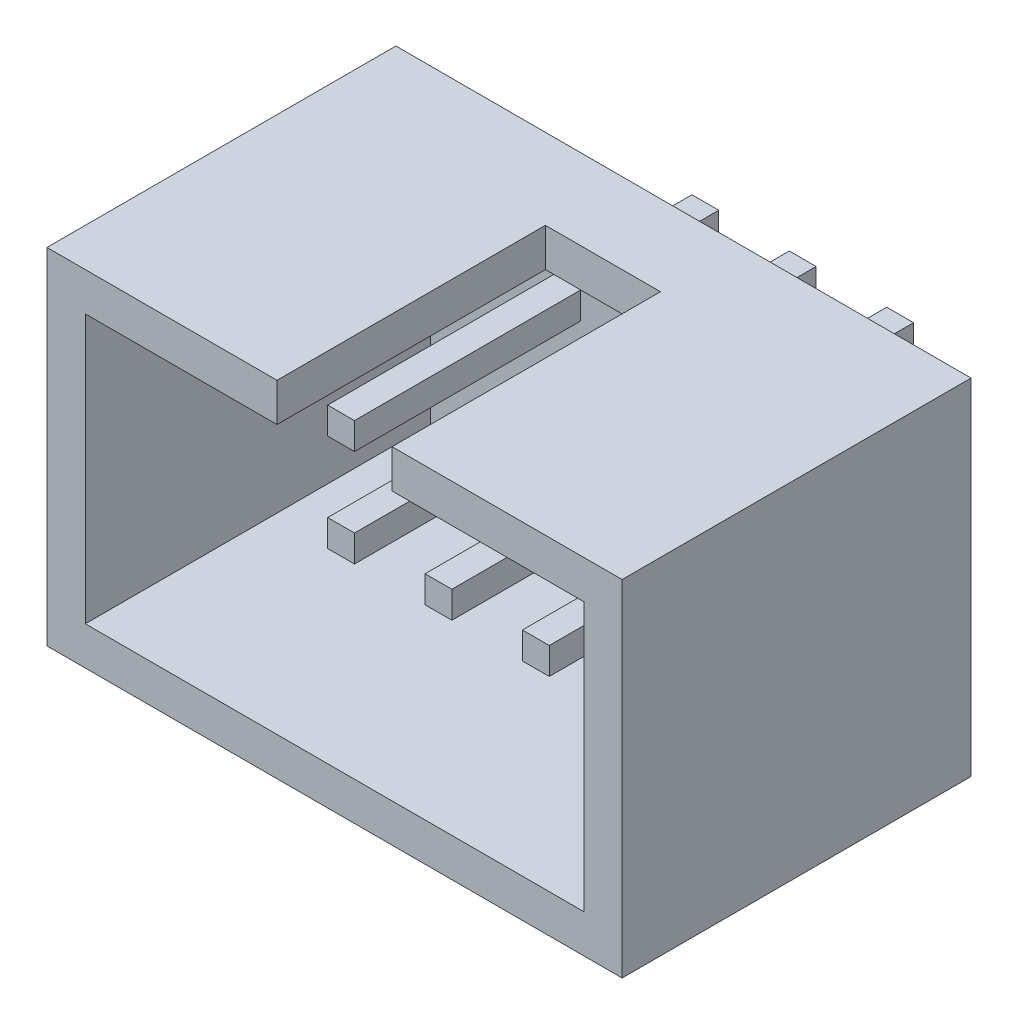
SolidWorks part; units mm, degrees
ref_plane "Alzado" through (0, 0, 0) normal (0, 0, 1) x (1, 0, 0)
ref_plane "Planta" through (0, 0, 0) normal (0, 1, 0) x (1, 0, 0)
ref_plane "Vista lateral" through (0, 0, 0) normal (1, 0, 0) x (0, 0, -1)
sketch "Croquis1" plane through (0, 0, 0) normal (0, 0, 1) x (1, 0, 0)
  line L13 (-6.5, -3.5) -> (-6.5, 3.5)
  line L14 (-7.5, -4.5) -> (7.5, -4.5)
  line L15 (-7.5, -4.5) -> (-7.5, 4.5)
  line L16 (-7.5, 4.5) -> (7.5, 4.5)
  line L17 (7.5, -4.5) -> (7.5, 4.5)
  line L18 (-7.5, -4.5) -> (7.5, 4.5) construction
  line L19 (-7.5, 4.5) -> (7.5, -4.5) construction
  line L20 (-6.5, 3.5) -> (6.5, 3.5)
  line L21 (6.5, -3.5) -> (6.5, 3.5)
  line L22 (-6.5, -3.5) -> (6.5, -3.5)
  point P0 (0, 0)
  dimension "D1" = 15
  dimension "D2" = 9
  dimension "D3" = 1
extrude "Saliente-Extruir1" add sketch "Croquis1" along normal blind 9
sketch "Croquis2" plane through (0, 0, 0) normal (0, 0, -1) x (-1, 0, 0)
  line L1 (-7.5, -4.5) -> (7.5, -4.5)
  line L2 (-7.5, -4.5) -> (-7.5, 4.5)
  line L3 (-7.5, 4.5) -> (7.5, 4.5)
  line L4 (7.5, -4.5) -> (7.5, 4.5)
  line L5 (-7.5, -4.5) -> (7.5, 4.5) construction
  line L6 (-7.5, 4.5) -> (7.5, -4.5) construction
  point P0 (0, 0)
extrude "Saliente-Extruir2" add sketch "Croquis2" along normal blind 0.1
sketch "Croquis3" plane through (0, 0, 9) normal (0, 0, 1) x (1, 0, 0)
  line L0 (6.5, 3.5) -> (-6.5, 3.5) construction
  line L1 (-1.5, 1.7962) -> (1.5, 1.7962)
  line L2 (-1.5, 1.7962) -> (-1.5, 5.2038)
  line L3 (-1.5, 5.2038) -> (1.5, 5.2038)
  line L4 (1.5, 1.7962) -> (1.5, 5.2038)
  line L5 (-1.5, 1.7962) -> (1.5, 5.2038) construction
  line L6 (-1.5, 5.2038) -> (1.5, 1.7962) construction
  point P0 (0, 3.5)
  point P7 (0, 3.5)
  dimension "D1" = 3
extrude "Cortar-Extruir1" cut sketch "Croquis3" against normal blind 7
sketch "Croquis4" plane through (0, 0, -0.1) normal (0, 0, -1) x (-1, 0, 0)
  line L0 (-7.5, 4.5) -> (-7.5, -4.5) construction
  line L1 (-2.5, 1.5) -> (-1.8, 1.5)
  line L2 (-2.5, 1.5) -> (-2.5, 0.8)
  line L3 (-2.5, 0.8) -> (-1.8, 0.8)
  line L4 (-1.8, 1.5) -> (-1.8, 0.8)
  line L5 (-2.5, 1.5) -> (-1.8, 0.8) construction
  line L6 (-2.5, 0.8) -> (-1.8, 1.5) construction
  line L7 (7.5, 4.5) -> (-7.5, 4.5) construction
  line L8 (0.04, 1.5) -> (0.04, 0.8)
  line L9 (0.04, 1.5) -> (0.74, 1.5)
  line L10 (0.74, 1.5) -> (0.74, 0.8)
  line L11 (0.04, 0.8) -> (0.74, 0.8)
  line L12 (2.58, 1.5) -> (2.58, 0.8)
  line L13 (2.58, 1.5) -> (3.28, 1.5)
  line L14 (3.28, 1.5) -> (3.28, 0.8)
  line L15 (2.58, 0.8) -> (3.28, 0.8)
  line L16 (0.04, -1.04) -> (0.04, -1.74)
  line L17 (0.04, -1.04) -> (0.74, -1.04)
  line L18 (0.74, -1.04) -> (0.74, -1.74)
  line L19 (0.04, -1.74) -> (0.74, -1.74)
  line L20 (2.58, -1.04) -> (2.58, -1.74)
  line L21 (2.58, -1.04) -> (3.28, -1.04)
  line L22 (3.28, -1.04) -> (3.28, -1.74)
  line L23 (2.58, -1.74) -> (3.28, -1.74)
  line L24 (-2.5, -1.04) -> (-2.5, -1.74)
  line L25 (-2.5, -1.04) -> (-1.8, -1.04)
  line L26 (-1.8, -1.04) -> (-1.8, -1.74)
  line L27 (-2.5, -1.74) -> (-1.8, -1.74)
  line L29 (0.74, 1.5) -> (0.04, 0.8) construction
  line L30 (0.04, 1.5) -> (0.74, 0.8) construction
  line L31 (0.74, -1.04) -> (0.04, -1.74) construction
  line L32 (0.04, -1.04) -> (0.74, -1.74) construction
  point P0 (-2.15, 1.15)
  dimension "D1" = 5
  dimension "D2" = 0.7
  dimension "D3" = 0.7
  dimension "D4" = 3
  dimension "D5" = 3
  dimension "D6" = 2
extrude "Saliente-Extruir3" add sketch "Croquis4" along normal blind 3.5 and the other way blind 6
